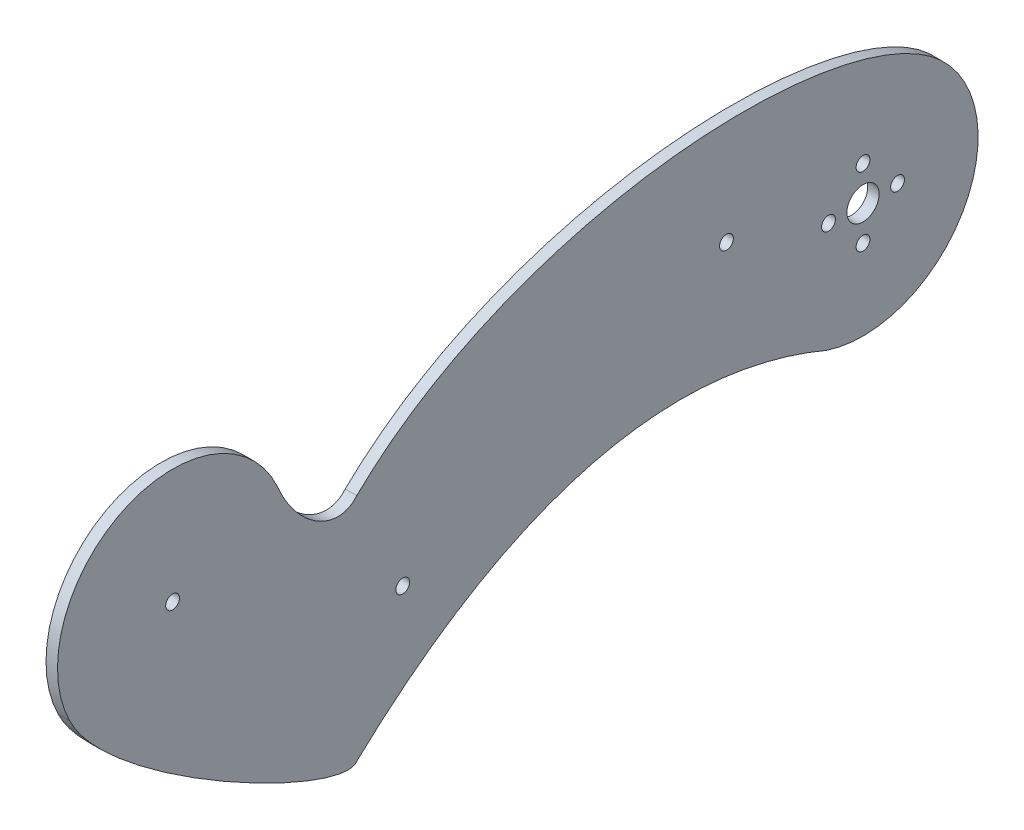
SolidWorks part; units mm, degrees
ref_plane "Alzado" through (0, 0, 0) normal (0, 0, 1) x (1, 0, 0)
ref_plane "Planta" through (0, 0, 0) normal (0, 1, 0) x (1, 0, 0)
ref_plane "Vista lateral" through (0, 0, 0) normal (1, 0, 0) x (0, 0, -1)
sketch "Croquis1" plane through (0, 0, 0) normal (1, 0, 0) x (0, 0, -1)
  line L0 (-150, 0) -> (-112.5, 0) construction
  line L1 (-150, 0) -> (-112.5, -50) construction
  line L2 (-112.5, -50) -> (0, 0) construction
  line L3 (0, 0) -> (-110, 0) construction
  line L4 (-112.5, 0) -> (-112.5, -50) construction
  arc A0 (-7.8546, -23.7341) -> (18.7736, 16.5092) centre (0, 0) ccw
  arc A1 (-127.1891, 10.2305) -> (-172.33, -11.2416) centre (-150, 0) ccw
  circle A2 centre (-150, 0) radius 1.5
  circle A3 centre (0, 0) radius 3.5
  circle A6 centre (-29.6616, 7.5) radius 1.5
  circle A7 centre (-7.5, 0) radius 1.5
  circle A8 centre (0, -7.5) radius 1.5
  circle A9 centre (0, 7.5) radius 1.5
  circle A10 centre (7.5, 0) radius 1.5
  circle A11 centre (-100, -22) radius 1.5
  spline S0 degree 3 poles (-110, 0) (-73.6737, 35.3013) (0.4829, 38.1328) (18.7736, 16.5092) knots 0 0 0 0 1 1 1 1
  spline S1 degree 3 poles (-110, 0) (-114.0627, -4.9396) (-122.9085, 0.0959) (-127.1891, 10.2305) knots 0 0 0 0 1 1 1 1
  spline S2 degree 3 poles (-110, -50) (-84.3133, -25.7703) (-48.9235, -6.3974) (-7.8546, -23.7341) knots 0 0 0 0 1 1 1 1
  spline S3 degree 3 poles (-110, -50) (-113.3631, -55.3095) (-164.149, -28.4002) (-172.33, -11.2416) knots 0 0 0 0 1 1 1 1
extrude "Saliente-Extruir1" add sketch "Croquis1" along normal blind 2.5
